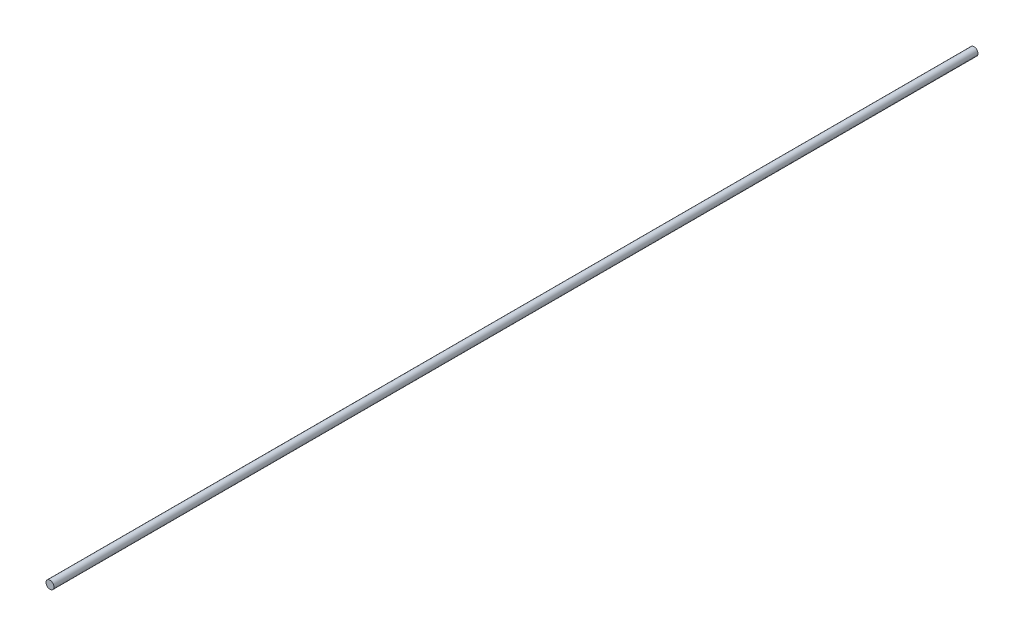
SolidWorks part; units mm, degrees
material "Stainless Steel (ferritic)"
ref_plane "Front Plane" through (0, 0, 0) normal (0, 0, 1) x (1, 0, 0)
ref_plane "Top Plane" through (0, 0, 0) normal (0, 1, 0) x (1, 0, 0)
ref_plane "Right Plane" through (0, 0, 0) normal (1, 0, 0) x (0, 0, -1)
sketch "Sketch1" plane through (0, 0, 0) normal (0, 0, 1) x (1, 0, 0)
  circle A0 centre (0, 0) radius 4
  dimension "D1" = 8
extrude "Boss-Extrude1" add sketch "Sketch1" along normal blind 930
